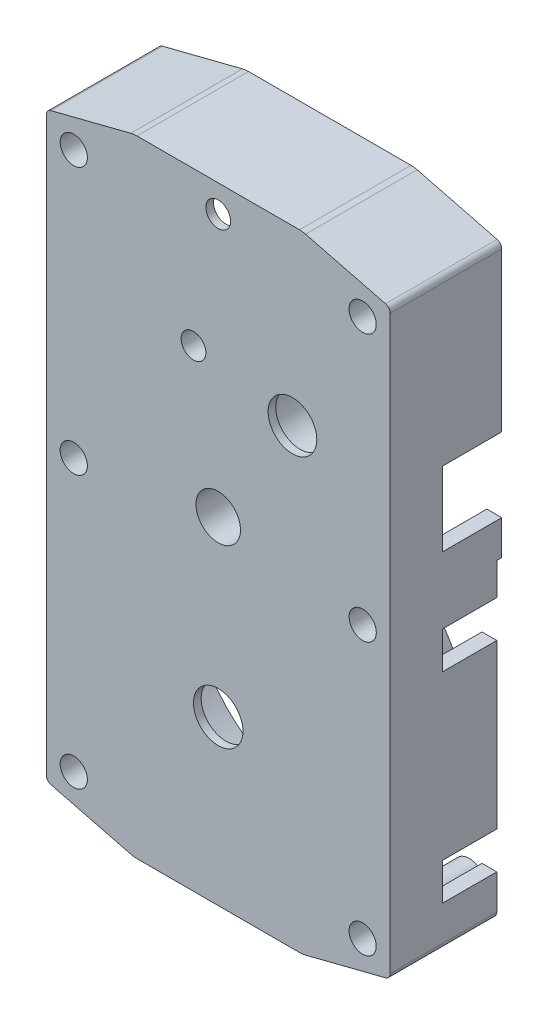
SolidWorks part; units mm, degrees
other "Camera1"
material "Polybutadiene (PB)"
ref_plane "Front Plane" through (0, 0, 0) normal (0, 0, 1) x (1, 0, 0)
ref_plane "Top Plane" through (0, 0, 0) normal (0, 1, 0) x (1, 0, 0)
ref_plane "Right Plane" through (0, 0, 0) normal (1, 0, 0) x (0, 0, -1)
sketch "Sketch4" plane through (0, 0, 0) normal (0, 0, 1) x (1, 0, 0)
  line L0 (0, 25.3) -> (0, 27.2341) construction
  line L1 (-3.6651, 0) -> (-10.2349, 0)
  line L2 (0, 1.0944) -> (0, 24.2056)
  line L3 (-3.6651, 25.3) -> (-10.2349, 25.3)
  line L4 (-13.9, 1.0944) -> (-13.9, 24.2056)
  line L5 (-3.54, 25.3) -> (-3.54, 27.2341) construction
  line L6 (-13.9, 24.2056) -> (-13.9, 27.2341) construction
  line L7 (-10.36, 25.3) -> (-10.36, 27.2341) construction
  line L8 (-13.9, 24.4) -> (13.315, 24.4) construction
  line L9 (-13.7116, 24.4479) -> (-10.4813, 25.2692)
  line L10 (-3.4187, 25.2692) -> (-0.1884, 24.4479)
  line L11 (-10.36, 27.2341) -> (-3.54, 27.2341) construction
  line L12 (-6.95, 27.2341) -> (-6.95, 25.3) construction
  line L13 (-0.1884, 24.4479) -> (-3.4187, 25.2692)
  line L14 (-10.2349, 0) -> (-6.95, 0) construction
  line L15 (-6.95, 0) -> (-6.95, 25.3) construction
  line L16 (-6.95, 12.65) -> (0, 12.65) construction
  line L17 (-3.4187, 0.0308) -> (-0.1884, 0.8521)
  line L18 (-3.6651, 0) -> (-10.2349, 0)
  line L19 (-13.7116, 0.8521) -> (-10.4813, 0.0308)
  arc A0 (-10.2349, 25.3) -> (-10.4813, 25.2692) centre (-10.2349, 24.3) ccw
  arc A1 (-13.7116, 24.4479) -> (-13.9, 24.2056) centre (-13.65, 24.2056) ccw
  arc A2 (-3.6651, 25.3) -> (-3.4187, 25.2692) centre (-3.6651, 24.3) cw
  arc A3 (-0.1884, 24.4479) -> (0, 24.2056) centre (-0.25, 24.2056) cw
  arc A4 (-0.1884, 0.8521) -> (0, 1.0944) centre (-0.25, 1.0944) ccw
  arc A5 (-3.6651, 0) -> (-3.4187, 0.0308) centre (-3.6651, 1) ccw
  arc A6 (-10.2349, 0) -> (-10.4813, 0.0308) centre (-10.2349, 1) cw
  arc A7 (-13.7116, 0.8521) -> (-13.9, 1.0944) centre (-13.65, 1.0944) cw
  dimension "D2" = 1
  dimension "D6" = 0.25
  dimension "D3" = 13.9
  dimension "D4" = 3.54
  dimension "D5" = 0.9
  dimension "D7" = 25.3
  dimension "D8" = 24.2056
  dimension "D9" = 24.4479
  dimension "D10" = 1.9341
extrude "Boss-Extrude1" add sketch "Sketch4" along normal blind 4.51 contours A7 L19 A6 L1 A5 L17 A4 L2 A3 L10 A2 L3 A0 L9 A1 L4
sketch "Sketch5" plane through (0, 0, 0) normal (0, 0, -1) x (-1, 0, 0)
  line L16 (13.3, 1.3665) -> (13.3, 23.9335)
  line L17 (13.3, 23.9335) -> (10.3334, 24.6877)
  line L18 (10.2349, 24.7) -> (3.6651, 24.7)
  line L19 (3.5666, 24.6877) -> (0.6, 23.9335)
  line L20 (0.6, 23.9335) -> (0.6, 1.3665)
  line L21 (0.6, 1.3665) -> (3.5666, 0.6123)
  line L22 (3.6651, 0.6) -> (10.2349, 0.6)
  line L23 (10.3334, 0.6123) -> (13.3, 1.3665)
  line L24 (13.3, 1.3665) -> (13.3, 23.9335)
  line L25 (13.3, 23.9335) -> (10.3334, 24.6877)
  line L26 (10.2349, 24.7) -> (3.6651, 24.7)
  line L27 (3.5666, 24.6877) -> (0.6, 23.9335)
  line L28 (0.6, 23.9335) -> (0.6, 1.3665)
  line L29 (0.6, 1.3665) -> (3.5666, 0.6123)
  line L30 (3.6651, 0.6) -> (10.2349, 0.6)
  line L31 (10.3334, 0.6123) -> (13.3, 1.3665)
  arc A16 (10.3334, 24.6877) -> (10.2349, 24.7) centre (10.2349, 24.3) ccw
  arc A17 (3.6651, 24.7) -> (3.5666, 24.6877) centre (3.6651, 24.3) ccw
  arc A18 (3.5666, 0.6123) -> (3.6651, 0.6) centre (3.6651, 1) ccw
  arc A19 (10.2349, 0.6) -> (10.3334, 0.6123) centre (10.2349, 1) ccw
  arc A20 (10.3334, 24.6877) -> (10.2349, 24.7) centre (10.2349, 24.3) ccw
  arc A21 (3.6651, 24.7) -> (3.5666, 24.6877) centre (3.6651, 24.3) ccw
  arc A22 (3.5666, 0.6123) -> (3.6651, 0.6) centre (3.6651, 1) ccw
  arc A23 (10.2349, 0.6) -> (10.3334, 0.6123) centre (10.2349, 1) ccw
  dimension "D1" = 0.6
extrude "Cut-Extrude1" cut sketch "Sketch5" against normal blind 4.2
sketch "Sketch6" plane through (0, 0, 4.2) normal (0, 0, -1) x (-1, 0, 0)
  line L0 (0.6, 23.9335) -> (0.6, 1.3665) construction
  line L1 (6.95, 24.7) -> (6.95, 0.6) construction
  line L2 (10.2349, 24.7) -> (3.6651, 24.7) construction
  line L3 (3.6651, 0.6) -> (10.2349, 0.6) construction
  circle A0 centre (1.1123, 1.7665) radius 0.65
  circle A1 centre (1.1123, 23.5335) radius 0.65
  circle A2 centre (1.11, 12.75) radius 0.65
  circle A3 centre (12.7877, 23.5335) radius 0.65
  circle A4 centre (12.7877, 1.7665) radius 0.65
  circle A5 centre (12.79, 12.75) radius 0.65
  dimension "D1" = 1.3
  dimension "D3" = 1.3
  dimension "D4" = 0.4
  dimension "D5" = 1.3
  dimension "D2" = 0.4
  dimension "D6" = 0.51
  dimension "D7" = 12.15
extrude "Boss-Extrude2" add sketch "Sketch6" along normal blind 4.2
sketch "Sketch7" plane through (0, 0, 0) normal (0, 0, -1) x (-1, 0, 0)
  line L0 (6.95, 24.7) -> (6.95, 0.6) construction
  line L1 (10.2349, 24.7) -> (3.6651, 24.7) construction
  line L2 (3.6651, 0.6) -> (10.2349, 0.6) construction
  circle A0 centre (1.1123, 1.7665) radius 0.55
  circle A1 centre (1.11, 12.75) radius 0.55
  circle A2 centre (1.1123, 23.5335) radius 0.55
  circle A3 centre (12.7877, 1.7665) radius 0.55
  circle A4 centre (12.7877, 23.5335) radius 0.55
  circle A5 centre (12.79, 12.75) radius 0.55
  dimension "D1" = 1.1
  dimension "D2" = 1.1
  dimension "D3" = 1.1
extrude "Cut-Extrude2" cut sketch "Sketch7" against normal blind 4.6
sketch "Sketch8" plane through (0, 0, 4.2) normal (0, 0, -1) x (-1, 0, 0)
  line L0 (10.2349, 24.7) -> (3.6651, 24.7) construction
  circle A0 centre (6.95, 24.2) radius 0.5
  point P6 (6.95, 24.7)
  dimension "D1" = 1
extrude "Cut-Extrude3" cut sketch "Sketch8" against normal blind 3.5
sketch "Sketch10" plane through (0, 0, 4.51) normal (0, 0, 1) x (1, 0, 0)
  line L0 (-6.95, 24.2) -> (-6.95, 19.1) construction
  line L1 (-6.95, 19.1) -> (-7.95, 19.1) construction
  line L2 (-7.95, 19.1) -> (-7.95, 18.3) construction
  line L3 (-7.95, 18.3) -> (-3.95, 18.3) construction
  line L4 (-3.6651, 0.6) -> (-10.2349, 0.6) construction
  line L5 (-6.95, 24.2) -> (-6.95, 13.6) construction
  line L6 (-6.95, 0) -> (-6.95, 6.6) construction
  line L7 (-3.6651, 0) -> (-10.2349, 0) construction
  line L8 (-6.95, 17.35) -> (-11.3, 17.35) construction
  circle A0 centre (-7.95, 19.1) radius 0.5
  circle A1 centre (-3.95, 18.3) radius 0.985
  circle A2 centre (-6.95, 13.6) radius 0.9
  circle A3 centre (-6.95, 6.6) radius 1
  circle A4 centre (-11.3, 17.35) radius 0.75
  dimension "D3" = 1
  dimension "D6" = 1.97
  dimension "D8" = 1.8
  dimension "D10" = 2
  dimension "D12" = 1.5
  dimension "D1" = 1
  dimension "D2" = 5.5
  dimension "D4" = 4.7
  dimension "D5" = 3
  dimension "D7" = 7
  dimension "D9" = 6
  dimension "D11" = 4.35
  dimension "D13" = 3.75
extrude "Cut-Extrude4" cut sketch "Sketch10" against normal blind 10
sketch "Sketch12" plane through (0, 25.3, 0) normal (0, 1, 0) x (1, 0, 0)
  line L0 (-4.489, 0) -> (0.8331, 0) construction
sketch "Sketch14" plane through (0, 0, 0) normal (1, 0, 0) x (0, 0, -1)
  line L0 (0, 23.9429) -> (0, 25.3) construction
  line L1 (0, 1.0944) -> (0, 24.2056) construction
sketch "Sketch16" plane through (0, 0, 0) normal (1, 0, 0) x (0, 0, -1)
  line L0 (0, 25.3) -> (-3.0579, 25.3) construction
  line L1 (0, 17.8) -> (-2.4, 17.8) construction
  line L2 (0, 1.0944) -> (0, 24.2056) construction
  line L3 (0, 17.8) -> (-2.4, 17.8)
  line L4 (-2.4, 17.8) -> (-2.4, 14.8)
  line L5 (-2.4, 14.8) -> (0, 14.8)
  line L6 (0, 14.8) -> (0, 17.8)
  line L7 (0, 12.1) -> (-2.4, 12.1)
  line L8 (0, 10.6) -> (-2.4, 10.6)
  line L9 (-2.4, 10.6) -> (-2.4, 4) construction
  line L10 (-2.4, 12.1) -> (-2.4, 10.6)
  line L11 (0, 12.1) -> (0, 10.6)
  line L12 (-2.4, 4) -> (0, 4)
  line L13 (0, 4) -> (0, 2.5)
  line L14 (0, 2.5) -> (-2.4, 2.5)
  line L15 (-2.4, 2.5) -> (-2.4, 4)
  line L16 (0, 0) -> (-2.4, 0) construction
  dimension "D1" = 4
  dimension "D2" = 2.4
  dimension "D3" = 3
  dimension "D4" = 2.7
  dimension "D5" = 6.6
  dimension "D6" = 1.5
  dimension "D7" = 1.5
extrude "Cut-Extrude5" cut sketch "Sketch16" against normal blind 0.6
sketch "Sketch17" plane through (0, 0, 0) normal (1, 0, 0) x (0, 0, -1)
  line L0 (0, 1.0944) -> (0, 0) construction
sketch "Sketch18" plane through (0, 0, 0) normal (0, -1, 0) x (-1, 0, 0)
  line L0 (3.6651, 0) -> (0, 0) construction
  line L1 (0, 0) -> (0, -3.4879) construction
  line L2 (3.7, 0) -> (3.7, -3.3667) construction
  line L3 (3.6651, 0) -> (10.2349, 0) construction
  line L4 (3.7, -2.5) -> (10.4, -2.5) construction
  line L5 (2.2, 0) -> (2.2, -2.4)
  line L6 (2.2, -2.4) -> (3.7, -2.4)
  line L7 (3.7, 0) -> (3.7, -2.4)
  line L8 (2.2, 0) -> (3.7, 0)
  line L9 (10.4, -2.5) -> (10.4, 0) construction
  line L10 (10.4, -2.4) -> (11.9, -2.4)
  line L11 (11.9, -2.4) -> (11.9, 0)
  line L12 (11.9, 0) -> (10.4, 0)
  line L13 (10.4, -2.4) -> (10.4, 0)
  dimension "D1" = 3.7
  dimension "D2" = 6.7
  dimension "D3" = 2.5
  dimension "D4" = 1.5
  dimension "D5" = 2.4
  dimension "D6" = 1.5
  dimension "D7" = 2.4
extrude "Cut-Extrude6" cut sketch "Sketch18" against normal blind 1
sketch "Sketch19" plane through (0, 0, 0) normal (0, -1, 0) x (-1, 0, 0)
  line L0 (3.8478, 0) -> (0, 0) construction
  line L1 (3.7, 0) -> (10.2349, 0) construction
  line L2 (0, 0) -> (0, -2.4389) construction
sketch "Sketch21" plane through (-13.9, 0, 0) normal (-1, 0, 0) x (0, 0, 1)
  line L0 (0, 0) -> (2.4, 0) construction
  line L1 (2.4, 0) -> (2.4, 4) construction
  line L2 (2.4, 4) -> (0, 4)
  line L3 (0, 1.0944) -> (0, 24.2056) construction
  line L4 (0, 4) -> (0, 2.5)
  line L5 (0, 2.5) -> (2.4, 2.5)
  line L6 (2.4, 2.5) -> (2.4, 4)
  line L7 (2.4, 4) -> (2.4, 10.6) construction
  line L8 (2.4, 10.6) -> (0, 10.6)
  line L9 (0, 10.6) -> (0, 12.1)
  line L10 (0, 12.1) -> (2.4, 12.1)
  line L11 (2.4, 12.1) -> (2.4, 10.6)
  line L12 (0, 25.3) -> (2.4, 25.3) construction
  line L13 (0, 22.3) -> (1.5, 22.3) construction
  line L14 (0, 22.3) -> (1.5, 22.3)
  line L15 (1.5, 22.3) -> (1.5, 14.05)
  line L16 (1.5, 14.05) -> (0, 14.05)
  line L17 (0, 14.05) -> (0, 22.3)
  dimension "D1" = 4
  dimension "D2" = 2.4
  dimension "D3" = 1.5
  dimension "D4" = 6.6
  dimension "D5" = 3
  dimension "D6" = 8.25
  dimension "D7" = 1.5
extrude "Cut-Extrude7" cut sketch "Sketch21" against normal blind 0.6
sketch "Sketch22" plane through (0, 0, 4.2) normal (0, 0, -1) x (-1, 0, 0)
  circle A2 centre (6.95, 13.6) radius 1.3
  circle A3 centre (6.95, 13.6) radius 0.9
  circle A4 centre (6.95, 13.6) radius 0.9 construction
  dimension "D1" = 0.4
extrude "Boss-Extrude3" add sketch "Sketch22" along normal blind 4.25
sketch "Sketch23" plane through (0, 0, 4.2) normal (0, 0, -1) x (-1, 0, 0)
  circle A0 centre (6.95, 6.6) radius 5.9
  circle A1 centre (6.95, 6.6) radius 5.5
  dimension "D1" = 0.4
  dimension "D2" = 11
extrude "Boss-Extrude4" add sketch "Sketch23" along normal blind 4
sketch "Sketch24" plane through (0, 0, 4.2) normal (0, 0, -1) x (-1, 0, 0)
  circle A0 centre (3.95, 18.3) radius 1.2
  circle A1 centre (3.95, 18.3) radius 1.6
  circle A2 centre (7.95, 19.1) radius 1.25
  circle A3 centre (7.95, 19.1) radius 0.5
  circle A4 centre (7.95, 19.1) radius 0.5 construction
  dimension "D1" = 2.4
  dimension "D2" = 0.4
  dimension "D3" = 0.75
extrude "Boss-Extrude5" add sketch "Sketch24" along normal blind 3.75
sketch "Sketch26" plane through (0, 0, 4.51) normal (0, 0, 1) x (1, 0, 0)
  circle A0 centre (-11.3, 17.35) radius 0.75
  circle A1 centre (-11.3, 17.35) radius 0.75 construction
extrude "Boss-Extrude6" add sketch "Sketch26" against normal blind 4.51
sketch "Sketch27" plane through (0, 0, 0) normal (0, 0, -1) x (-1, 0, 0)
  circle A0 centre (11.3, 17.35) radius 0.675
  dimension "D1" = 1.35
extrude "Boss-Extrude7" add sketch "Sketch27" along normal blind 4.6
sketch "Sketch28" plane through (0, 0, 0.45) normal (0, 0, -1) x (-1, 0, 0)
  arc A0 (7.7371, 20.3317) -> (7.95, 17.85) centre (7.95, 19.1) cw
  circle A1 centre (7.95, 19.1) radius 1.25 construction
  arc A2 (7.7371, 20.1607) -> (7.95, 18.0181) centre (7.95, 19.1) cw
  arc A3 (7.95, 17.85) -> (7.95, 18.0181) centre (7.95, 17.9341) cw
  arc A4 (7.7371, 20.1607) -> (7.7371, 20.3317) centre (8.1633, 20.2462) cw
  dimension "D1" = 1.0819
  dimension "D2" = 0.2133
  dimension "D3" = 0.4346
extrude "Boss-Extrude8" add sketch "Sketch28" along normal blind 1.25
sketch "Sketch29" plane through (0, 0, 0) normal (1, 0, 0) x (0, 0, -1)
  line L0 (0, 0) -> (0, 13.4) construction
  line L1 (0, 4) -> (0, 10.6) construction
  line L2 (0, 13.4) -> (-0.2, 13.4)
  line L3 (-0.2, 13.4) -> (-0.2, 0)
  line L4 (0, 0) -> (-2.4389, 0) construction
  line L5 (-0.2, 0) -> (0, 0)
  line L6 (0, 0) -> (0, 13.4)
  dimension "D1" = 13.4
  dimension "D2" = 0.2
extrude "Cut-Extrude8" cut sketch "Sketch29" against normal blind 15
